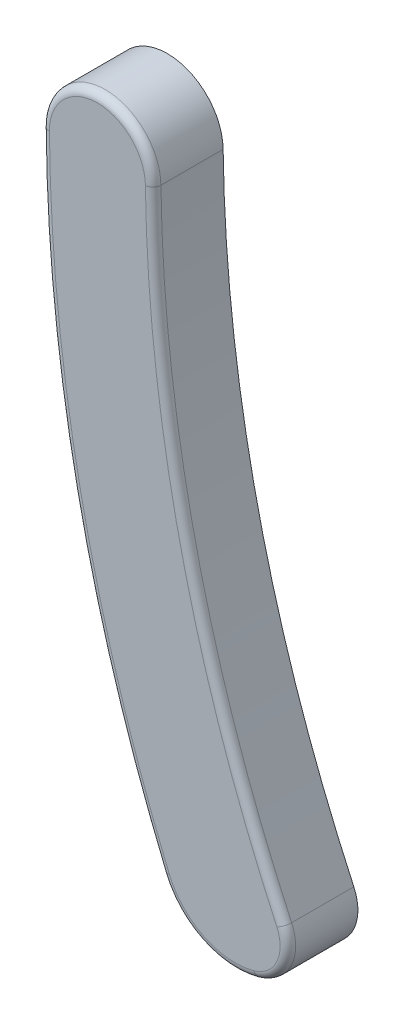
SolidWorks part; units mm, degrees
ref_plane "前视基准面" through (0, 0, 0) normal (0, 0, 1) x (1, 0, 0)
ref_plane "上视基准面" through (0, 0, 0) normal (0, 1, 0) x (1, 0, 0)
ref_plane "右视基准面" through (0, 0, 0) normal (1, 0, 0) x (0, 0, -1)
sketch "Sketch1" plane through (0, 0, 0) normal (0, 0, 1) x (1, 0, 0)
  arc A5 (-0.7466, 18.6904) -> (7.6588, -18.181) centre (89.5456, 19.88) ccw
  arc A6 (5.8662, -22.0484) -> (7.6588, -18.181) centre (5.1282, -19.3572) ccw
  arc A7 (-0.1701, -19.1093) -> (5.8662, -22.0484) centre (4.5211, -17.1428) ccw
  arc A8 (-7.9187, 18.6137) -> (-0.1701, -19.1093) centre (91.778, 19.4347) ccw
  arc A9 (-0.7466, 18.6904) -> (-7.9187, 18.6137) centre (-4.3325, 18.6432) ccw
extrude "Extrude1" add sketch "Sketch1" along normal blind 4.5
fillet "Fillet1" radius 0.5 5 edges at (7.66, -20.5307, 4.5) (2.2943, -21.7162, 4.5) (-5.8831, -0.6255, 4.5) (-4.3709, 22.2293, 4.5) (1.5043, -0.1902, 4.5)
